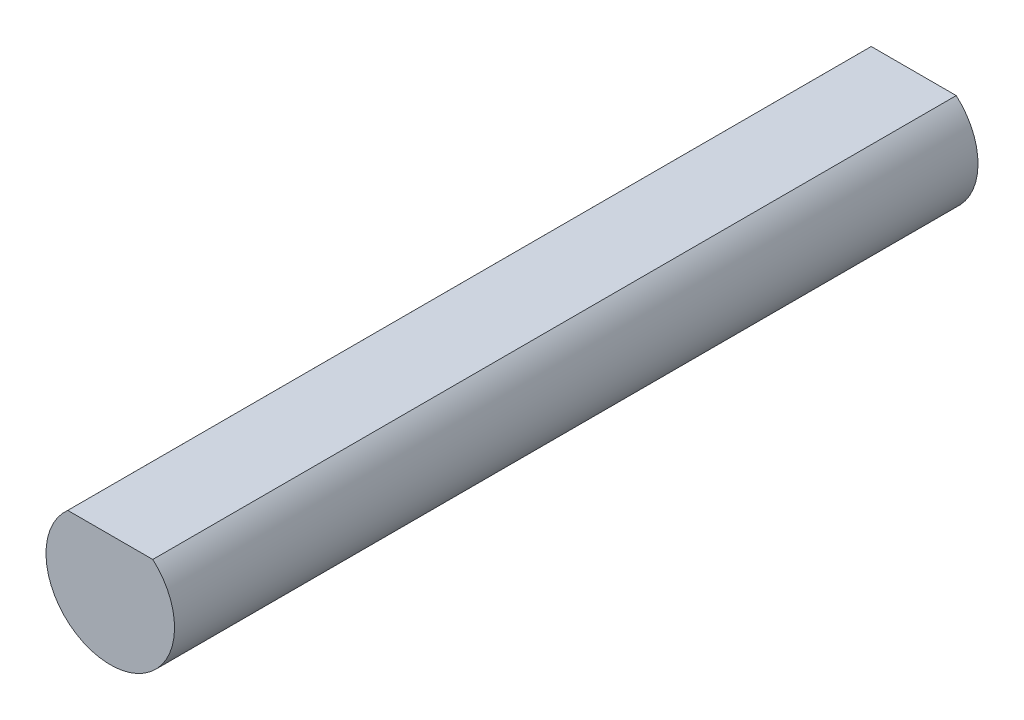
SolidWorks part; units mm, degrees
ref_plane "Front Plane" through (0, 0, 0) normal (0, 0, 1) x (1, 0, 0)
ref_plane "Top Plane" through (0, 0, 0) normal (0, 1, 0) x (1, 0, 0)
ref_plane "Right Plane" through (0, 0, 0) normal (1, 0, 0) x (0, 0, -1)
sketch "Sketch1" plane through (0, 0, 0) normal (0, 0, 1) x (1, 0, 0)
  line L0 (-1.3229, 1.5) -> (1.3229, 1.5)
  arc A0 (1.3229, 1.5) -> (-1.3229, 1.5) centre (0, 0) cw
  point P4 (-7.8238, 1.3297)
  dimension "D1" = 2
  dimension "D2" = 1.5
extrude "Boss-Extrude1" add sketch "Sketch1" along normal blind 25
